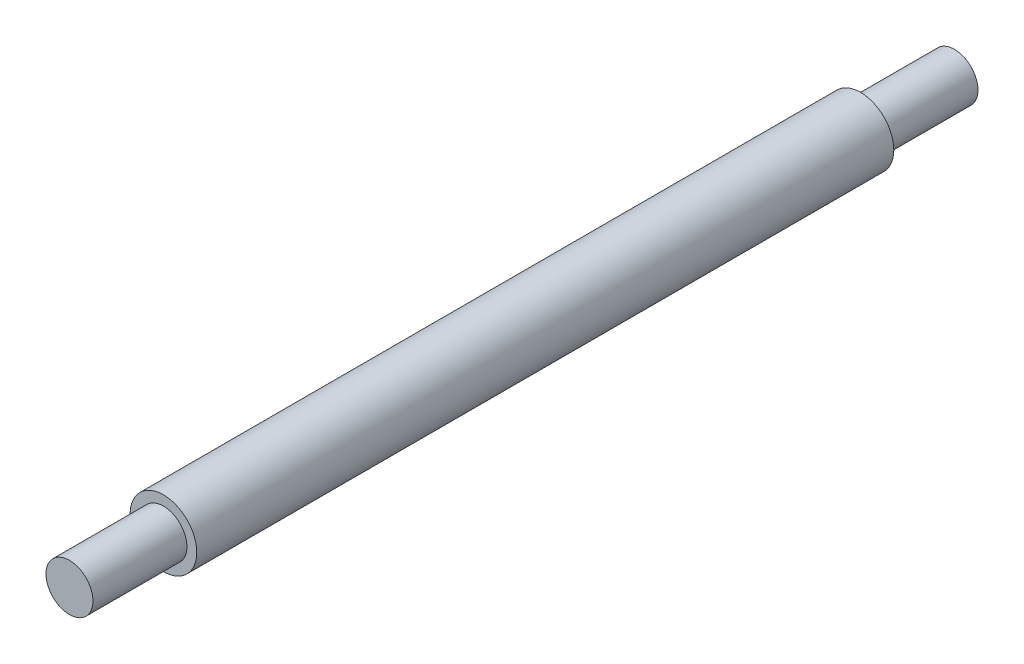
SolidWorks part; units mm, degrees
ref_plane "Front Plane" through (0, 0, 0) normal (0, 0, 1) x (1, 0, 0)
ref_plane "Top Plane" through (0, 0, 0) normal (0, 1, 0) x (1, 0, 0)
ref_plane "Right Plane" through (0, 0, 0) normal (1, 0, 0) x (0, 0, -1)
sketch "Sketch1" plane through (0, 0, 0) normal (1, 0, 0) x (0, 0, -1)
  line L0 (0, 0) -> (113, 0) construction
  line L1 (0, 0) -> (0, 3)
  line L2 (0, 3) -> (12, 3)
  line L3 (12, 3) -> (12, 4.25)
  line L4 (12, 4.25) -> (101, 4.25)
  line L5 (101, 4.25) -> (101, 3)
  line L6 (101, 3) -> (113, 3)
  line L7 (113, 3) -> (113.0634, 2.9859)
  line L8 (113, 3) -> (113, 0)
  dimension "D1" = 113
  dimension "D2" = 12
  dimension "D3" = 12
  dimension "D4" = 6
  dimension "D5" = 8.5
  dimension "D6" = 6
revolve "Revolve2" add sketch "Sketch1" angle 360 about L0
